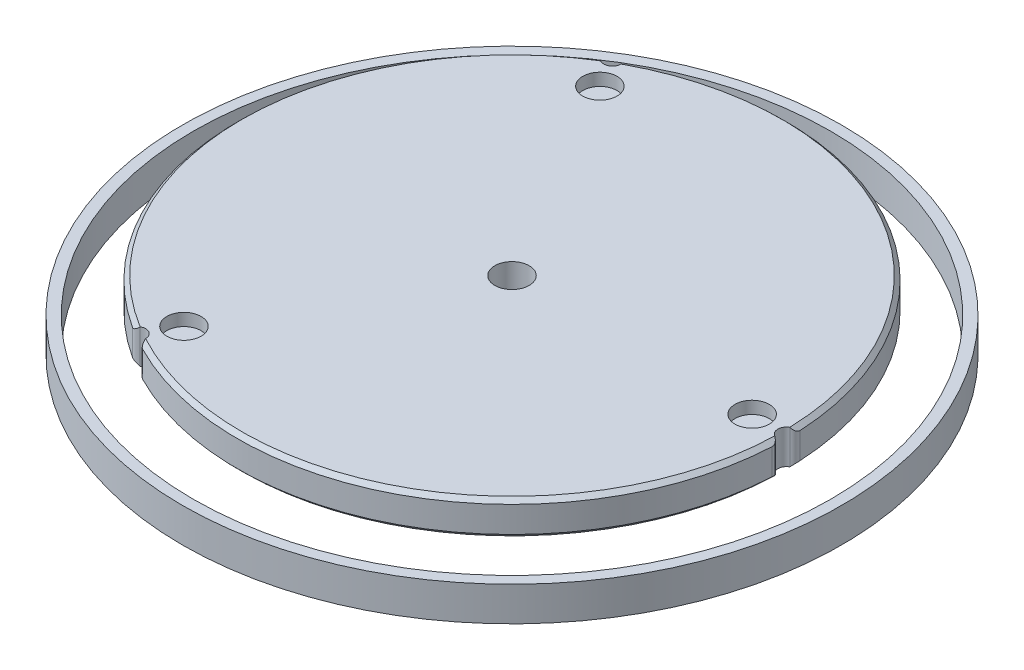
SolidWorks part; units mm, degrees
ref_plane "Front Plane" through (0, 0, 0) normal (0, 0, 1) x (1, 0, 0)
ref_plane "Top Plane" through (0, 0, 0) normal (0, 1, 0) x (1, 0, 0)
ref_plane "Right Plane" through (0, 0, 0) normal (1, 0, 0) x (0, 0, -1)
sketch "Sketch1" plane through (0, 0, 0) normal (0, 1, 0) x (1, 0, 0)
  circle A0 centre (0, 0) radius 50.8
  dimension "D1" = 101.6
extrude "Boss-Extrude1" add sketch "Sketch1" along normal blind 6.35
sketch "Sketch2" plane through (0, 6.35, 0) normal (0, 1, 0) x (1, 0, 0)
  line L0 (0, 0) -> (44.45, 0) construction
  line L1 (0, 0) -> (-22.225, 38.4948) construction
  line L2 (0, 0) -> (-22.225, -38.4948) construction
  circle A0 centre (0, 0) radius 44.45 construction
  circle A1 centre (-22.225, -38.4948) radius 3.175
  circle A2 centre (-22.225, 38.4948) radius 3.175
  circle A3 centre (44.45, 0) radius 3.175
  dimension "D1" = 88.9
  dimension "D4" = 6.35
  dimension "D2" = 120
  dimension "D3" = 120
extrude "Cut-Extrude1" cut sketch "Sketch2" against normal blind 2.286
sketch "Sketch3" plane through (0, 6.35, 0) normal (0, 1, 0) x (1, 0, 0)
  circle A0 centre (0, 0) radius 3.175
  dimension "D1" = 6.35
extrude "Cut-Extrude2" cut sketch "Sketch3" against normal through all both and the other way through all
sketch "Sketch4" plane through (0, 0, 0) normal (0, -1, 0) x (1, 0, 0)
  line L0 (0, 0) -> (44.45, 0) construction
  line L1 (0, 0) -> (-22.225, -38.4948) construction
  line L2 (0, 0) -> (-22.225, 38.4948) construction
  circle A0 centre (50.8, 0) radius 1.5875
  circle A1 centre (0, 0) radius 50.8 construction
  circle A2 centre (-25.4, 43.9941) radius 1.5875
  circle A3 centre (-25.4, -43.9941) radius 1.5875
  dimension "D1" = 3.175
extrude "Cut-Extrude3" cut sketch "Sketch4" against normal through all
chamfer "Chamfer1" distance 0.762 angle 45 6 edges at (25.4, 6.35, 43.9941) (25.4, 0, 43.9941) (-50.8, 0, 0) (-50.8, 6.35, 0) (25.4, 6.35, -43.9941) (25.4, 0, -43.9941)
fillet "Fillet1" radius 1.27 6 edges at (-24.013, 3.175, 44.7663) (-26.7622, 3.175, 43.179) (50.7752, 3.175, -1.5873) (50.7752, 3.175, 1.5873) (-24.013, 3.175, -44.7663) (-26.7622, 3.175, -43.179)
sketch "Sketch5" plane through (0, 0, 0) normal (0, -1, 0) x (1, 0, 0)
  circle A0 centre (0, 0) radius 61
  circle A1 centre (0, 0) radius 59
  dimension "D1" = 122
  dimension "D2" = 118
extrude "Boss-Extrude2" add sketch "Sketch5" along normal blind 6.35
